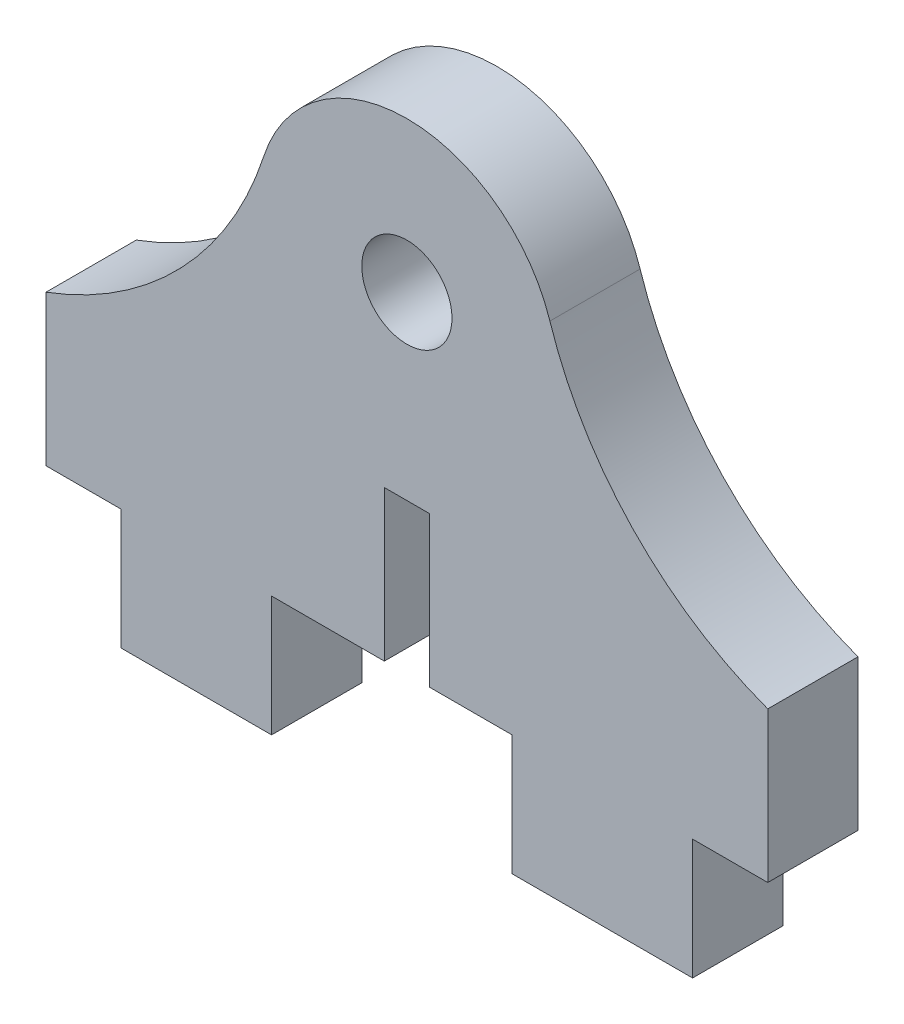
SolidWorks part; units mm, degrees
material "PMMA"
ref_plane "Front Plane" through (0, 0, 0) normal (0, 0, 1) x (1, 0, 0)
ref_plane "Top Plane" through (0, 0, 0) normal (0, 1, 0) x (1, 0, 0)
ref_plane "Right Plane" through (0, 0, 0) normal (1, 0, 0) x (0, 0, -1)
sketch "Sketch1" plane through (0, 0, 0) normal (0, 0, 1) x (1, 0, 0)
  line L0 (0, 0) -> (0, -5.5) construction
  line L1 (-1.25, -11) -> (-7, -11)
  line L2 (-12, -11) -> (-12, -6)
  line L3 (1.25, -11) -> (6, -11)
  line L4 (6, -11) -> (6, -22.5)
  line L5 (8.5, -25) -> (9.5, -25)
  line L6 (12, -22.5) -> (12, -6)
  line L7 (-1.25, -11) -> (-1.25, -5.5)
  line L8 (-1.25, -5.5) -> (1.25, -5.5)
  line L9 (1.25, -5.5) -> (1.25, -11)
  line L10 (-12, -11) -> (-12, -15)
  line L11 (-12, -15) -> (-7, -15)
  line L12 (-7, -15) -> (-7, -11)
  circle A0 centre (0, 0) radius 1.5
  arc A1 (4.7553, 1.545) -> (-4.7553, 1.545) centre (0, 0) ccw
  arc A2 (-12, -6) -> (-4.7553, 1.545) centre (-16.1681, 5.2529) ccw
  arc A3 (12, -6) -> (4.7553, 1.545) centre (16.1681, 5.2529) cw
  arc A4 (12, -22.5) -> (9.5, -25) centre (9.5, -22.5) cw
  arc A5 (8.5, -25) -> (6, -22.5) centre (8.5, -22.5) cw
  circle A6 centre (9, -22) radius 1
  point P20 (12, -25)
  point P23 (6, -25)
  dimension "D1" = 3
  dimension "D2" = 11
  dimension "D6" = 12
  dimension "D3" = 5
  dimension "D13" = 2.5
  dimension "D15" = 2
  dimension "D4" = 11
  dimension "D5" = 5
  dimension "D7" = 12
  dimension "D8" = 6
  dimension "D9" = 2.5
  dimension "D10" = 1.25
  dimension "D11" = 5.5
  dimension "D12" = 14
  dimension "D14" = 11
  dimension "D16" = 9
  dimension "D17" = 5
  dimension "D18" = 4
  dimension "D19" = 15
extrude "Boss-Extrude1" add sketch "Sketch1" along normal blind 3
sketch "Sketch2" plane through (0, 0, 3) normal (0, 0, 1) x (1, 0, 0)
  line L1 (-7, -15) -> (14.2153, -15)
  line L2 (-7, -15) -> (-7, -25.6208)
  line L3 (-7, -25.6208) -> (14.2153, -25.6208)
  line L4 (14.2153, -15) -> (14.2153, -25.6208)
extrude "Cut-Extrude1" cut sketch "Sketch2" against normal through all
sketch "Sketch3" plane through (0, 0, 3) normal (0, 0, 1) x (1, 0, 0)
  line L0 (9.5, -15) -> (9.5, -11)
  line L1 (12, -15) -> (6, -15) construction
  line L2 (9.5, -11) -> (12, -11)
  line L3 (12, -15) -> (12, -6) construction
  line L4 (12, -11) -> (12, -15)
  line L5 (12, -15) -> (9.5, -15)
  line L6 (-12, -15) -> (-12, -11)
  line L7 (-12, -15) -> (-9.5, -15)
  line L8 (-12, -11) -> (-9.5, -11)
  line L9 (-9.5, -15) -> (-9.5, -11)
  line L10 (-12, -6) -> (-12, -15) construction
  dimension "D1" = 4
  dimension "D2" = 2.5
  dimension "D3" = 2.5
extrude "Cut-Extrude2" cut sketch "Sketch3" against normal blind 10
sketch "Sketch4" plane through (0, 0, 3) normal (0, 0, 1) x (1, 0, 0)
  line L0 (1.25, -11) -> (6, -11) construction
  line L1 (-7, -11) -> (-4.5, -11)
  line L2 (-7, -11) -> (-7, -15)
  line L3 (-7, -15) -> (-4.5, -15)
  line L4 (-4.5, -11) -> (-4.5, -15)
  line L5 (6, -15) -> (3.5, -15)
  line L6 (6, -15) -> (6, -11)
  line L7 (6, -11) -> (3.5, -11)
  line L8 (3.5, -15) -> (3.5, -11)
  dimension "D1" = 4
  dimension "D2" = 2.5
  dimension "D3" = 2.5
extrude "Boss-Extrude2" add sketch "Sketch4" against normal up to surface (3 mm away) up to face at (-0.1111, -9.2287, 0)
sketch "Sketch5" plane through (0, 0, 0) normal (0, 0, -1) x (-1, 0, 0)
  line L1 (-1.25, -5.5) -> (1.25, -5.5)
  line L2 (-1.25, -5.5) -> (-1.25, -11)
  line L3 (-1.25, -11) -> (1.25, -11)
  line L4 (1.25, -5.5) -> (1.25, -11)
extrude "Boss-Extrude3" add sketch "Sketch5" against normal up to surface (3 mm away) up to face at (-0.1111, -9.2287, 3)
sketch "Sketch6" plane through (0, 0, 0) normal (0, 0, -1) x (-1, 0, 0)
  line L0 (4.5, -11) -> (-3.5, -11) construction
  line L1 (0.75, -16) -> (-0.75, -16)
  line L2 (0.75, -16) -> (0.75, -6)
  line L3 (0.75, -6) -> (-0.75, -6)
  line L4 (-0.75, -16) -> (-0.75, -6)
  line L5 (0.75, -16) -> (-0.75, -6) construction
  line L6 (0.75, -6) -> (-0.75, -16) construction
  point P0 (0, -11)
  dimension "D1" = 10
  dimension "D2" = 1.5
extrude "Cut-Extrude3" cut sketch "Sketch6" against normal blind 5
